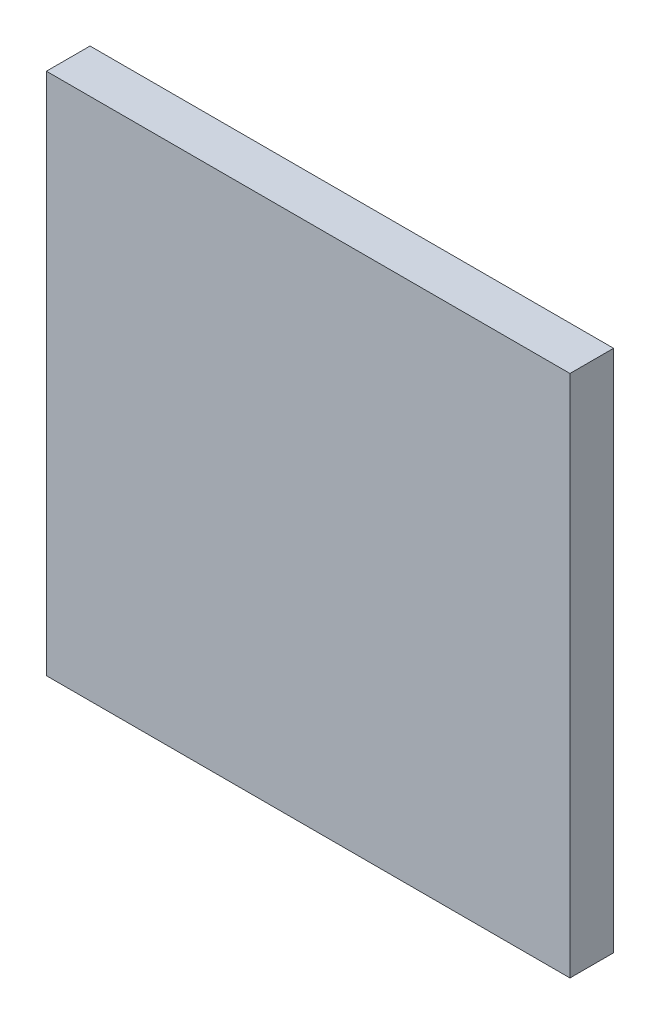
SolidWorks part; units mm, degrees
ref_plane "Front Plane" through (0, 0, 0) normal (0, 0, 1) x (1, 0, 0)
ref_plane "Top Plane" through (0, 0, 0) normal (0, 1, 0) x (1, 0, 0)
ref_plane "Right Plane" through (0, 0, 0) normal (1, 0, 0) x (0, 0, -1)
sketch "Sketch1" plane through (0, 0, 0) normal (0, 0, 1) x (1, 0, 0)
  line L0 (27.8837, 0) -> (-26.4754, 0) construction
  line L1 (-152.4, 152.4) -> (152.4, 152.4)
  line L2 (-152.4, 152.4) -> (-152.4, -152.4)
  line L3 (-152.4, -152.4) -> (152.4, -152.4)
  line L4 (152.4, 152.4) -> (152.4, -152.4)
  line L5 (0, 20.9832) -> (0, -19.5749) construction
  dimension "D1" = 304.8
extrude "Extrude1" add sketch "Sketch1" against normal blind 25.4
